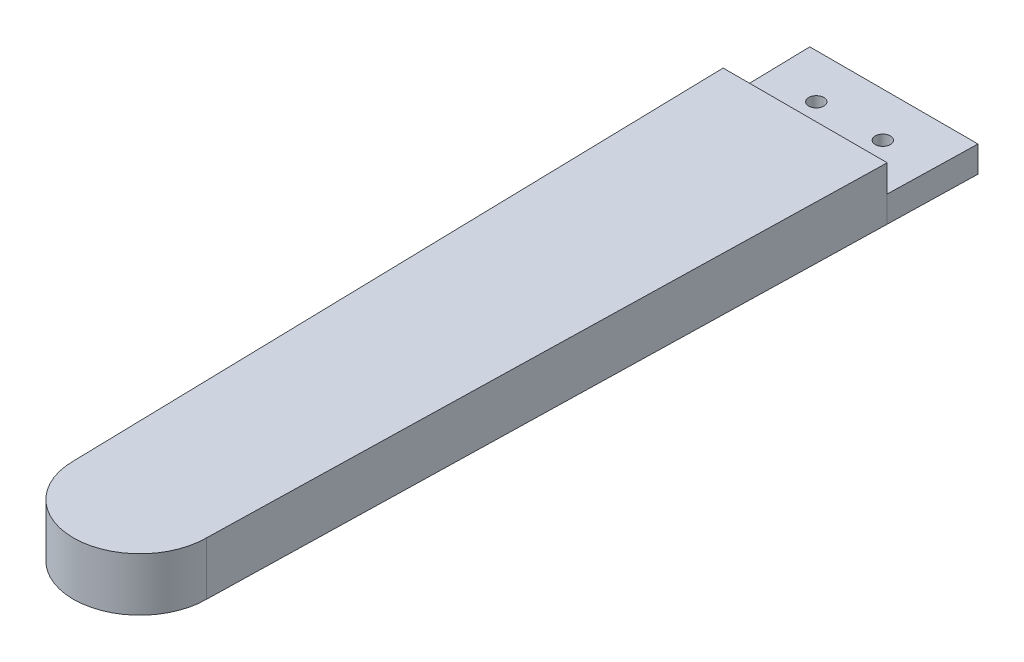
SolidWorks part; units mm, degrees
ref_plane "Front Plane" through (0, 0, 0) normal (0, 0, 1) x (1, 0, 0)
ref_plane "Top Plane" through (0, 0, 0) normal (0, 1, 0) x (1, 0, 0)
ref_plane "Right Plane" through (0, 0, 0) normal (1, 0, 0) x (0, 0, -1)
sketch "Sketch1" plane through (0, 0, 0) normal (0, 1, 0) x (1, 0, 0)
  line L0 (0, 75) -> (0, -75) construction
  line L1 (-18.5, 75) -> (18.5, 75)
  line L2 (-18.5, 75) -> (-15, -75)
  line L3 (18.5, 75) -> (15, -75)
  circle A0 centre (0, -75) radius 15
  point P4 (0, 0)
  point P8 (0, 75)
  dimension "D3" = 30
  dimension "D1" = 37
  dimension "D2" = 150
extrude "Boss-Extrude1" add sketch "Sketch1" along normal blind 12
sketch "Sketch2" plane through (0, 0, 0) normal (0, -1, 0) x (1, 0, 0)
  line L0 (0, -75) -> (0, -95) construction
  line L1 (-18.5, -75) -> (18.5, -75) construction
  line L2 (18.965, -95) -> (-18.965, -95)
  line L3 (-18.965, -95) -> (-18.5, -75)
  line L4 (18.5, -75) -> (18.965, -95)
  line L5 (-18.5, -75) -> (18.5, -75)
  line L8 (-15, 75) -> (-18.5, -75)
  line L9 (-18.5, -75) -> (18.5, -75)
  line L10 (18.5, -75) -> (15, 75)
  line L11 (-15, 75) -> (-18.5, -75)
  line L13 (18.5, -75) -> (15, 75)
  arc A1 (15, 75) -> (-15, 75) centre (0, 75) ccw
  arc A2 (15, 75) -> (-15, 75) centre (0, 75) ccw
  point P8 (0, -95)
  point P11 (-27.6507, -95)
  line M11 (-18.5, -75) -> (18.5, -75)
  dimension "D1" = 20
  dimension "D2" = 37.93
  dimension "D3" = 0
extrude "Boss-Extrude2" add sketch "Sketch2" against normal blind 5.9 contours L5 L0 L2 L4 | L0 L3 L2 M11
sketch "Sketch3" plane through (0, 0, 0) normal (0, -1, 0) x (1, 0, 0)
  line L0 (0, -95) -> (0, -85) construction
  line L1 (18.965, -95) -> (-18.965, -95) construction
  line L2 (7.5, -85) -> (-7.5, -85) construction
  circle A0 centre (-7.5, -85) radius 1.7
  circle A1 centre (7.5, -85) radius 1.7
  point P8 (0, -85)
  dimension "D1" = 10
  dimension "D2" = 15
extrude "Cut-Extrude1" cut sketch "Sketch3" against normal blind 5.9
sketch "Sketch4" plane through (0, 0, 0) normal (0, -1, 0) x (1, 0, 0)
  line L1 (-7.5, -81.7668) -> (-10.3, -83.3834)
  line L2 (-10.3, -83.3834) -> (-10.3, -86.6166)
  line L3 (-10.3, -86.6166) -> (-7.5, -88.2332)
  line L4 (-7.5, -88.2332) -> (-4.7, -86.6166)
  line L5 (-4.7, -86.6166) -> (-4.7, -83.3834)
  line L6 (-4.7, -83.3834) -> (-7.5, -81.7668)
  line L7 (7.5, -81.7668) -> (4.7, -83.3834)
  line L8 (4.7, -83.3834) -> (4.7, -86.6166)
  line L9 (4.7, -86.6166) -> (7.5, -88.2332)
  line L10 (7.5, -88.2332) -> (10.3, -86.6166)
  line L11 (10.3, -86.6166) -> (10.3, -83.3834)
  line L12 (10.3, -83.3834) -> (7.5, -81.7668)
  circle A0 centre (-7.5, -85) radius 2.8 construction
  circle A1 centre (7.5, -85) radius 2.8 construction
extrude "Cut-Extrude2" cut sketch "Sketch4" against normal blind 3
